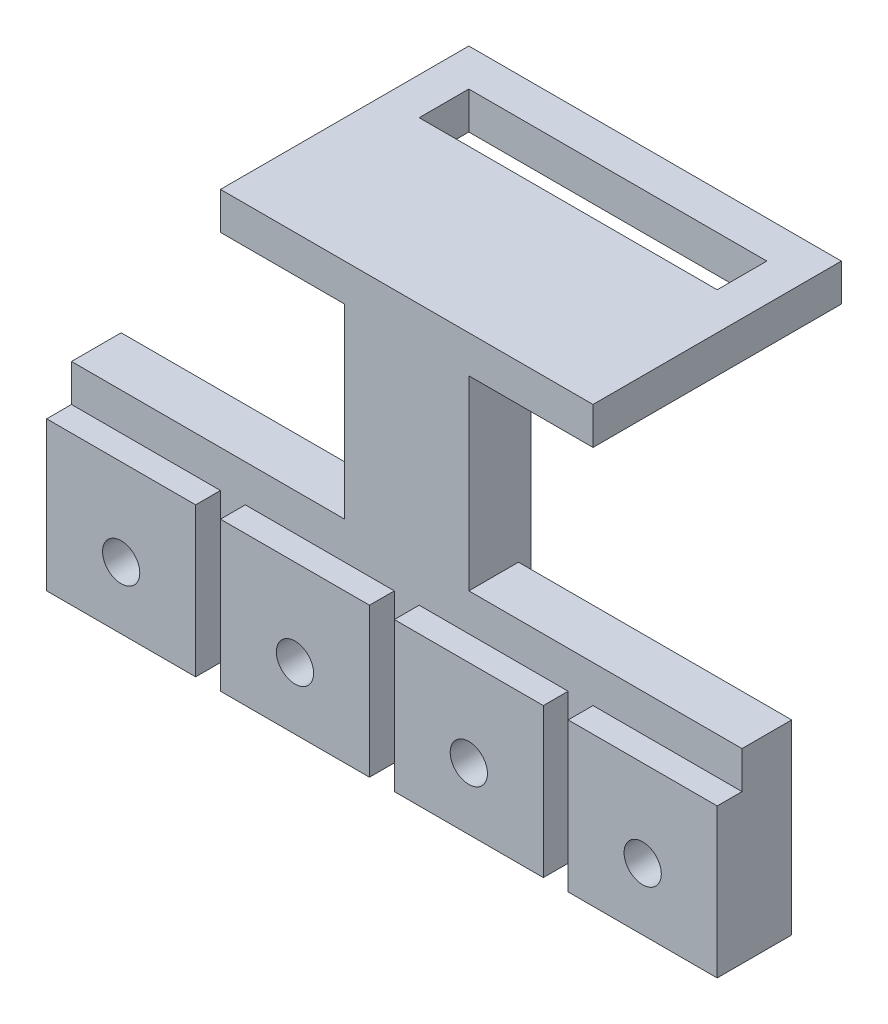
SolidWorks part; units mm, degrees
ref_plane "Front Plane" through (0, 0, 0) normal (0, 0, 1) x (1, 0, 0)
ref_plane "Top Plane" through (0, 0, 0) normal (0, 1, 0) x (1, 0, 0)
ref_plane "Right Plane" through (0, 0, 0) normal (1, 0, 0) x (0, 0, -1)
sketch "Sketch1" plane through (0, 0, 0) normal (0, 0, 1) x (1, 0, 0)
  line L1 (-4.3316, 2.5829) -> (7.6684, 2.5829)
  line L2 (-4.3316, 2.5829) -> (-4.3316, -9.4171)
  line L3 (-4.3316, -9.4171) -> (7.6684, -9.4171)
  line L4 (7.6684, 2.5829) -> (7.6684, -9.4171)
  dimension "D1" = 12
  dimension "D2" = 12
extrude "Boss-Extrude1" add sketch "Sketch1" along normal blind 2
sketch "Sketch2" plane through (0, 0, 0) normal (0, 0, -1) x (-1, 0, 0)
  line L1 (4.3316, -9.4171) -> (-49.6684, -9.4171)
  line L2 (4.3316, -9.4171) -> (4.3316, 5.5829)
  line L3 (4.3316, 5.5829) -> (-49.6684, 5.5829)
  line L4 (-49.6684, -9.4171) -> (-49.6684, 5.5829)
  dimension "D1" = 54
  dimension "D2" = 15
extrude "Boss-Extrude2" add sketch "Sketch2" along normal blind 4
sketch "Sketch3" plane through (0, 0, 0) normal (0, 0, 1) x (1, 0, 0)
  line L0 (49.6684, -9.4171) -> (7.6684, -9.4171) construction
  line L1 (9.6684, 2.5829) -> (21.6684, 2.5829)
  line L2 (9.6684, 2.5829) -> (9.6684, -9.4171)
  line L3 (9.6684, -9.4171) -> (21.6684, -9.4171)
  line L4 (21.6684, 2.5829) -> (21.6684, -9.4171)
  line L5 (7.6684, -9.4171) -> (7.6684, 2.5829) construction
  line L7 (23.6684, 2.5829) -> (35.6684, 2.5829)
  line L8 (23.6684, 2.5829) -> (23.6684, -9.4171)
  line L9 (23.6684, -9.4171) -> (35.6684, -9.4171)
  line L10 (35.6684, 2.5829) -> (35.6684, -9.4171)
  line L11 (37.6684, -9.4171) -> (49.6684, -9.4171)
  line L12 (37.6684, -9.4171) -> (37.6684, 2.5829)
  line L13 (37.6684, 2.5829) -> (49.6684, 2.5829)
  line L14 (49.6684, -9.4171) -> (49.6684, 2.5829)
  dimension "D1" = 2
  dimension "D2" = 12
  dimension "D3" = 12
  dimension "D4" = 2
  dimension "D5" = 12
  dimension "D6" = 12
  dimension "D7" = 2
  dimension "D8" = 12
  dimension "D9" = 12
extrude "Boss-Extrude3" add sketch "Sketch3" along normal blind 2
sketch "Sketch4" plane through (0, 0, 2) normal (0, 0, 1) x (1, 0, 0)
  line L0 (-4.3316, 2.5829) -> (-4.3316, -9.4171) construction
  line L1 (7.6684, 2.5829) -> (-4.3316, 2.5829) construction
  circle A0 centre (1.6684, -4.4171) radius 1.5
  circle A1 centre (15.6684, -4.4171) radius 1.5
  circle A2 centre (29.6684, -4.4171) radius 1.5
  circle A3 centre (43.6684, -4.4171) radius 1.5
  dimension "D1" = 3
  dimension "D2" = 6
  dimension "D3" = 7
  dimension "D4" = 4
extrude "Cut-Extrude1" cut sketch "Sketch4" against normal blind 9
sketch "Sketch5" plane through (0, 5.5829, 0) normal (0, 1, 0) x (1, 0, 0)
  line L0 (-4.3316, 0) -> (49.6684, 0) construction
  line L1 (17.6684, 5) -> (27.6684, 5)
  line L2 (17.6684, 5) -> (17.6684, 0)
  line L3 (17.6684, 0) -> (27.6684, 0)
  line L4 (27.6684, 5) -> (27.6684, 0)
  line L5 (-4.3316, 4) -> (-4.3316, 0) construction
  dimension "D1" = 22
  dimension "D2" = 10
  dimension "D3" = 5
extrude "Boss-Extrude4" add sketch "Sketch5" along normal blind 15 and the other way blind 5
sketch "Sketch6" plane through (0, 20.5829, 0) normal (0, 1, 0) x (1, 0, 0)
  line L0 (-4.3316, 0) -> (17.6684, 0) construction
  line L1 (7.6684, 0) -> (37.6684, 0)
  line L2 (7.6684, 0) -> (7.6684, 20)
  line L3 (7.6684, 20) -> (37.6684, 20)
  line L4 (37.6684, 0) -> (37.6684, 20)
  line L5 (-4.3316, 4) -> (-4.3316, 0) construction
  dimension "D1" = 20
  dimension "D2" = 30
  dimension "D3" = 12
extrude "Boss-Extrude5" add sketch "Sketch6" along normal blind 3
sketch "Sketch7" plane through (0, 23.5829, 0) normal (0, 1, 0) x (1, 0, 0)
  line L0 (7.6684, 20) -> (7.6684, 0) construction
  line L1 (10.6684, 17) -> (34.6684, 17)
  line L2 (10.6684, 17) -> (10.6684, 13)
  line L3 (10.6684, 13) -> (34.6684, 13)
  line L4 (34.6684, 17) -> (34.6684, 13)
  line L5 (37.6684, 20) -> (7.6684, 20) construction
  dimension "D1" = 4
  dimension "D2" = 24
  dimension "D3" = 3
  dimension "D4" = 3
extrude "Cut-Extrude2" cut sketch "Sketch7" against normal blind 3
